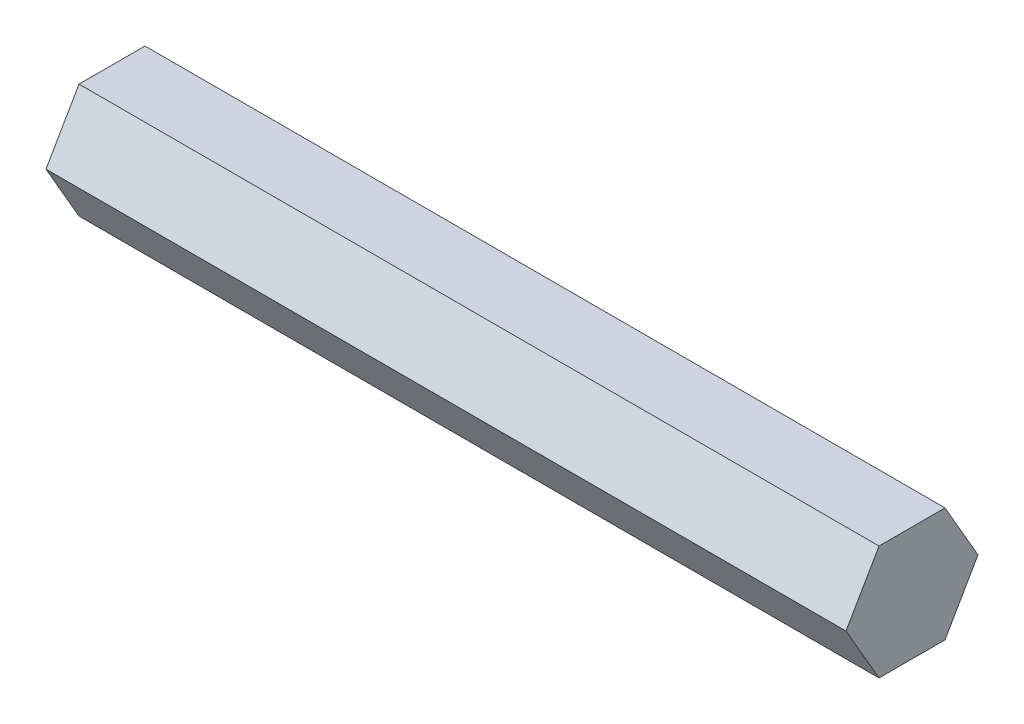
SolidWorks part; units mm, degrees
material "6061-T6 (SS)"
ref_plane "Front Plane" through (0, 0, 0) normal (0, 0, 1) x (1, 0, 0)
ref_plane "Top Plane" through (0, 0, 0) normal (0, 1, 0) x (1, 0, 0)
ref_plane "Right Plane" through (0, 0, 0) normal (1, 0, 0) x (0, 0, -1)
sketch "Sketch1" plane through (0, 0, 0) normal (1, 0, 0) x (0, 0, -1)
  line L1 (-7.3323, 0) -> (-3.6662, -6.35)
  line L2 (-3.6662, -6.35) -> (3.6662, -6.35)
  line L3 (3.6662, -6.35) -> (7.3323, 0)
  line L4 (7.3323, 0) -> (3.6662, 6.35)
  line L5 (3.6662, 6.35) -> (-3.6662, 6.35)
  line L6 (-3.6662, 6.35) -> (-7.3323, 0)
  circle A0 centre (0, 0) radius 6.35 construction
  dimension "D1" = 12.7
extrude "Boss-Extrude1" add sketch "Sketch1" along normal blind 88.9
